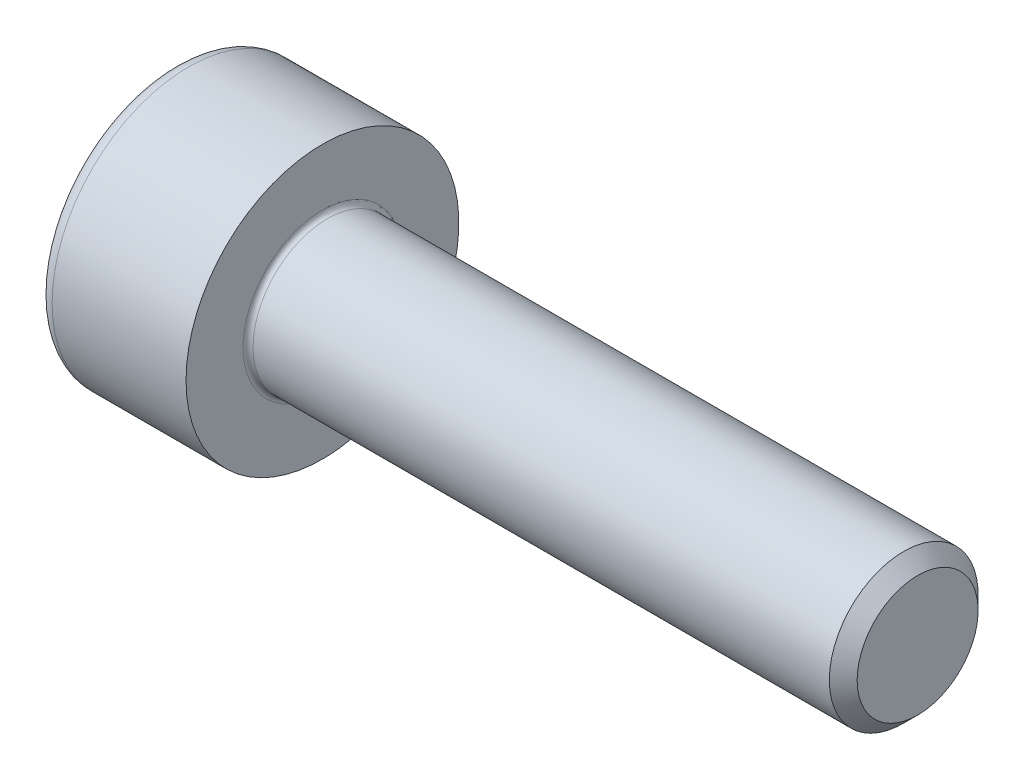
SolidWorks part; units mm, degrees
ref_plane "Plane1" through (0, 0, 0) normal (0, 0, 1) x (1, 0, 0)
ref_plane "Plane2" through (0, 0, 0) normal (0, 1, 0) x (1, 0, 0)
ref_plane "Plane3" through (0, 0, 0) normal (1, 0, 0) x (0, 0, -1)
sketch "BodySke" plane through (0, 0, 0) normal (0, 0, 1) x (1, 0, 0)
  line L0 (0, 0) -> (0, 2.75)
  line L1 (0, 2.75) -> (3, 2.75)
  line L2 (3, 2.75) -> (3, 1.5)
  line L3 (3, 1.5) -> (14.7195, 1.5)
  line L4 (15, 1.2195) -> (15, 0)
  line L5 (15, 0) -> (0, 0)
  line L6 (-31.75, 0) -> (127, 0) construction
  line L8 (15, 1.2195) -> (14.7195, 1.5)
  line L10 (15, -1.2195) -> (14.7195, -1.5) construction
  line L11 (3.5, 9.525) -> (3.5, 3.175) construction
  line L12 (3, 9.525) -> (3, 3.175) construction
  line L13 (-45, 9.525) -> (-45, 3.175) construction
  dimension "Diameter" = 3
  dimension "Head_ht" = 3
  dimension "Length" = 12
  dimension "Body_ch_ang" = 45
  dimension "Head_dia" = 5.5
  dimension "Minor_dia" = 2.439
  dimension "Advance" = 0.5
  dimension "Thread_nom" = 12
  dimension "Thread_length" = 60
revolve "Base-Revolve" add sketch "BodySke"
cosmetic thread "ThreadCosmetic" [suppressed]
fillet "Fillet1" radius 0.1 1 edges at (3, 0, 1.5)
fillet "Fillet2" radius 0.3 1 edges at (0, 0, 2.75)
sketch "Sketch2" plane through (0, 0, 0) normal (0, 0, 1) x (1, 0, 0)
  line L0 (0, 1.26) -> (1.3, 1.26)
  line L1 (1.3, 1.26) -> (2.0275, 0)
  line L2 (-31.75, 0) -> (127, 0) construction
  line L3 (2.0275, 0) -> (0, 0)
  line L4 (0, 0) -> (0, 1.26)
  line L6 (0, 0) -> (47.625, 0) construction
  dimension "D1" = 1.26
  dimension "D2" = 60
  dimension "Depth" = 1.3
revolve "Hex-PreBroach" cut sketch "Sketch2" angle 360 about L6
sketch "Sketch3" plane through (0, 0, 0) normal (-1, 0, 0) x (0, 0.5, 0.866)
  line L0 (0.7275, 1.26) -> (-0.7275, 1.26)
  line L1 (-0.7275, 1.26) -> (-1.4549, 0)
  line L2 (0.7275, 1.26) -> (1.4549, 0)
  line L3 (0.7275, -1.26) -> (1.4549, 0)
  line L4 (0.7275, -1.26) -> (-0.7275, -1.26)
  line L5 (-0.7275, -1.26) -> (-1.4549, 0)
  dimension "D1" = 1.26
  dimension "D2" = 1.26
  dimension "Hex_size" = 2.52
extrude "Hex" cut sketch "Sketch3" against normal blind 1.3
sketch "ThdSchSke" plane through (0, 0, 0) normal (0, 0, 1) x (1, 0, 0)
  line L0 (4.5, -1.2195) -> (4.3036, -1.5)
  line L1 (4.5, -1.2195) -> (4.6964, -1.5)
  line L2 (4.6964, -1.5) -> (4.6964, -1.875)
  line L3 (-3.175, 0) -> (5.1513, 0) construction
  line L4 (0, 2.45) -> (0, -2.45) construction
  line L5 (4.6964, -1.875) -> (4.3036, -1.875)
  line L6 (4.3036, -1.875) -> (4.3036, -1.5)
  dimension "Thread_minor" = 2.439
  dimension "Diameter" = 3
  dimension "Start" = 4.5
  dimension "SideAngle" = 55
  dimension "VeeAngle" = 70
  dimension "Overcut" = 3.75
revolve "ThreadSchematic" [suppressed] cut sketch "ThdSchSke" angle 360 about L3
pattern_linear "ThdSchPat" [suppressed]
equation "\"D2@Sketch3\" = \"Hex_size@Sketch3\" / 2"
equation "\"D1@Sketch3\" = \"Hex_size@Sketch3\" / 2"
equation "\"D1@Sketch2\" = \"Hex_size@Sketch3\" / 2"
equation "\"Thread_minor@ThreadCosmetic\"  =  \"Minor_dia@BodySke\""
equation "\"Depth@Sketch2\" =  \"Key_eng@Hex\""
equation "\"Thread_length@ThreadCosmetic\" = ((sgn( (\"Length@BodySke\" - \"Advance@BodySke\" * 3.0) - \"Thread_nom@BodySke\" )-1)*( (\"Length@BodySke\" - \"Advance@BodySke\" * 3.0) - \"Thread_nom@BodySke\" ))/-2+ \"Thread_nom@BodySke\""
equation "\"Thread_minor@ThdSchSke\" = \"Minor_dia@BodySke\""
equation "\"Diameter@ThdSchSke\" = \"Diameter@BodySke\""
equation "\"Overcut@ThdSchSke\" = \"Diameter@BodySke\" * 1.25"
equation "\"Start@ThdSchSke\" = \"Head_ht@BodySke\" + \"Length@BodySke\" - \"Thread_length@ThreadCosmetic\"  '---Non-countersunk---"
equation "\"Num_threads@ThdSchPat\" = int( \"Thread_length@ThreadCosmetic\" / \"Advance@BodySke\" + 0.999 )  + 1"
equation "\"Advance@ThdSchPat\" = \"Thread_length@ThreadCosmetic\" /  (\"Num_threads@ThdSchPat\" - 1) 'relax it"
equation "\"Num_threads@ThdSchPat\" = \"Num_threads@ThdSchPat\" - sgn( \"Num_threads@ThdSchPat\" - 1) '---chamfered tips only---"
